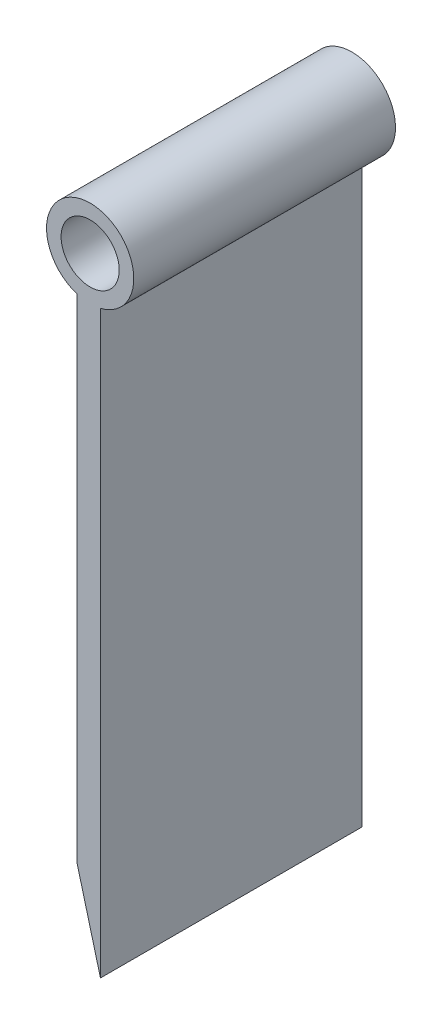
SolidWorks part; units mm, degrees
ref_plane "Alzado" through (0, 0, 0) normal (0, 0, 1) x (1, 0, 0)
ref_plane "Planta" through (0, 0, 0) normal (0, 1, 0) x (1, 0, 0)
ref_plane "Vista lateral" through (0, 0, 0) normal (1, 0, 0) x (0, 0, -1)
sketch "Croquis1" plane through (0, 0, 0) normal (0, 0, 1) x (1, 0, 0)
  line L4 (0, 0) -> (0, 49.8563)
  line L6 (-2, 49.9192) -> (-2, 7.5)
  line L7 (-2, 7.5) -> (0, 0)
  circle A0 centre (-0.8864, 53.5) radius 2.5
  arc A1 (0, 49.8563) -> (-2, 49.9192) centre (-0.8864, 53.5) ccw
  point P9 (0, 0)
  dimension "D4" = 7.5
  dimension "D5" = 5
extrude "Saliente-Extruir2" add sketch "Croquis1" along normal blind 22.5
